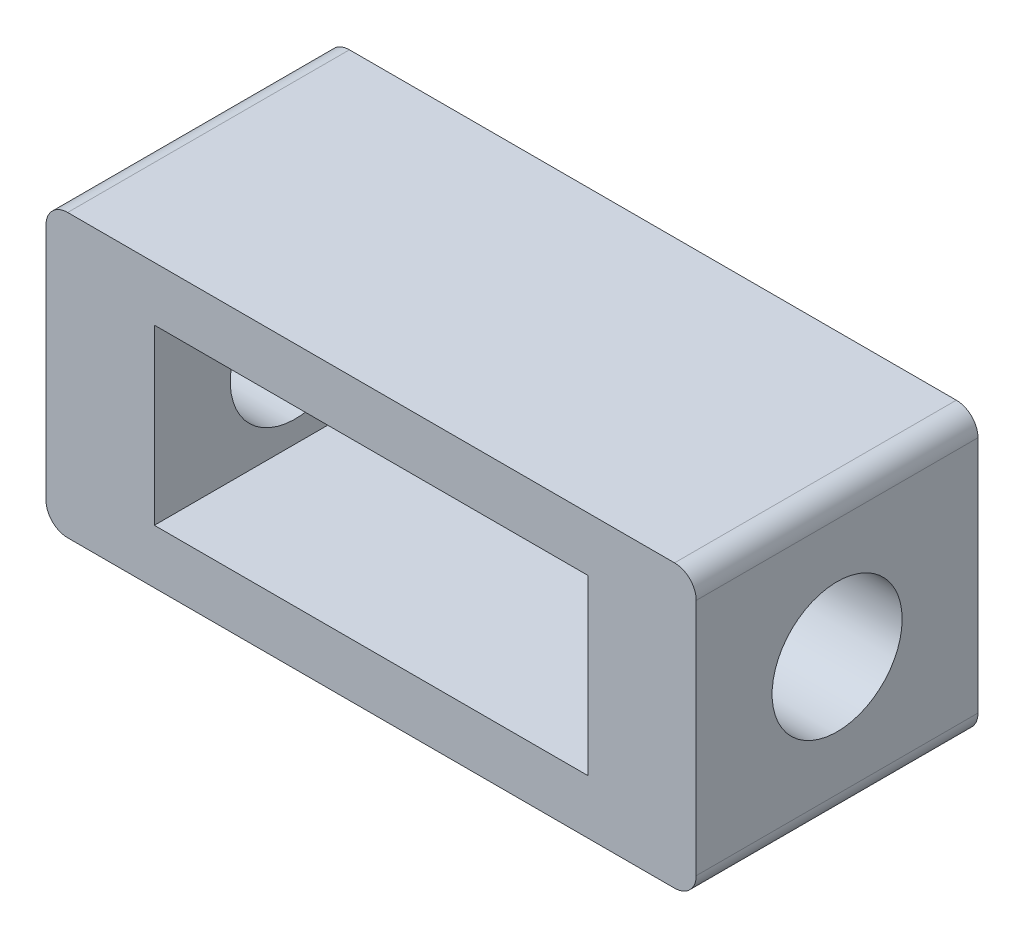
SolidWorks part; units mm, degrees
material "PET"
ref_plane "Front Plane" through (0, 0, 0) normal (0, 0, 1) x (1, 0, 0)
ref_plane "Top Plane" through (0, 0, 0) normal (0, 1, 0) x (1, 0, 0)
ref_plane "Right Plane" through (0, 0, 0) normal (1, 0, 0) x (0, 0, -1)
sketch "Sketch1" plane through (0, 0, 0) normal (0, 0, 1) x (1, 0, 0)
  line L1 (2, 0) -> (58, 0)
  line L2 (0, 2) -> (0, 24)
  line L3 (2, 26) -> (58, 26)
  line L4 (60, 2) -> (60, 24)
  line L5 (10, 21) -> (50, 21)
  line L6 (10, 21) -> (10, 5)
  line L7 (10, 5) -> (50, 5)
  line L8 (50, 21) -> (50, 5)
  arc A1 (0, 24) -> (2, 26) centre (2, 24) cw
  arc A2 (2, 0) -> (0, 2) centre (2, 2) cw
  arc A3 (58, 0) -> (60, 2) centre (58, 2) ccw
  arc A4 (58, 26) -> (60, 24) centre (58, 24) cw
  point P7 (0, 26)
  point P10 (0, 0)
  point P13 (60, 0)
  point P20 (60, 13)
  point P21 (50, 13)
  dimension "D4" = 16
  dimension "D3" = 2
  dimension "D1" = 60
  dimension "D2" = 26
  dimension "D5" = 10
  dimension "D6" = 10
extrude "Boss-Extrude1" add sketch "Sketch1" along normal blind 26
sketch "Sketch5" plane through (0, 0, 0) normal (0, 0, -1) x (-1, 0, 0)
  line L0 (-4, 22) -> (-56, 22)
  line L2 (-56, 4) -> (-4, 4)
  line L3 (-4, 4) -> (-4, 22)
  line L4 (-2, 26) -> (-58, 26)
  line L5 (-60, 24) -> (-60, 2)
  line L6 (-58, 0) -> (-2, 0)
  line L7 (0, 2) -> (0, 24)
  line L8 (-2, 26) -> (-58, 26)
  line L9 (-60, 24) -> (-60, 2)
  line L10 (-58, 0) -> (-2, 0)
  line L11 (0, 2) -> (0, 24)
  line L16 (-56, 22) -> (-56, 4) construction
  arc A0 (-4, 22) -> (-4, 22) centre (-4, 22) ccw
  arc A1 (-56, 22) -> (-56, 22) centre (-56, 22) ccw
  arc A2 (-56, 4) -> (-56, 4) centre (-56, 4) ccw
  arc A3 (-4, 4) -> (-4, 4) centre (-4, 4) ccw
  arc A4 (0, 24) -> (-2, 26) centre (-2, 24) ccw
  arc A5 (-58, 26) -> (-60, 24) centre (-58, 24) ccw
  arc A6 (-60, 2) -> (-58, 0) centre (-58, 2) ccw
  arc A7 (-2, 0) -> (0, 2) centre (-2, 2) ccw
  arc A8 (0, 24) -> (-2, 26) centre (-2, 24) ccw
  arc A9 (-58, 26) -> (-60, 24) centre (-58, 24) ccw
  arc A10 (-60, 2) -> (-58, 0) centre (-58, 2) ccw
  arc A11 (-2, 0) -> (0, 2) centre (-2, 2) ccw
  dimension "D1" = 0
  dimension "D2" = 4
sketch "Sketch6" plane through (60, 0, 0) normal (1, 0, 0) x (0, 0, -1)
  line L0 (-26, 2) -> (-26, 24) construction
  circle A0 centre (-13, 13) radius 6
  point P4 (-26, 13)
  dimension "D1" = 12
  dimension "D2" = 13
extrude "Cut-Extrude1" cut sketch "Sketch6" against normal through all
